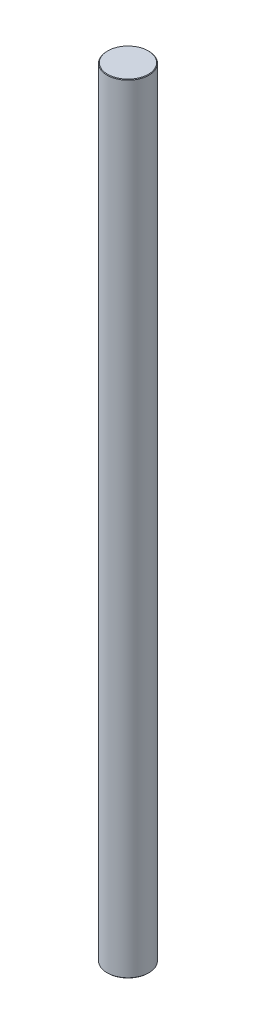
SolidWorks part; units mm, degrees
ref_plane "Front Plane" through (0, 0, 0) normal (0, 0, 1) x (1, 0, 0)
ref_plane "Top Plane" through (0, 0, 0) normal (0, 1, 0) x (1, 0, 0)
ref_plane "Right Plane" through (0, 0, 0) normal (1, 0, 0) x (0, 0, -1)
sketch "Sketch1" plane through (0, 0, 0) normal (0, 1, 0) x (1, 0, 0)
  circle A0 centre (0, 0) radius 4.7625
  dimension "D1" = 9.525
extrude "Boss-Extrude1" add sketch "Sketch1" along normal blind 177.8
chamfer "Chamfer1" distance 0.127 angle 45 2 edges at (0, 0, 4.7625) (0, 177.8, 4.7625)
